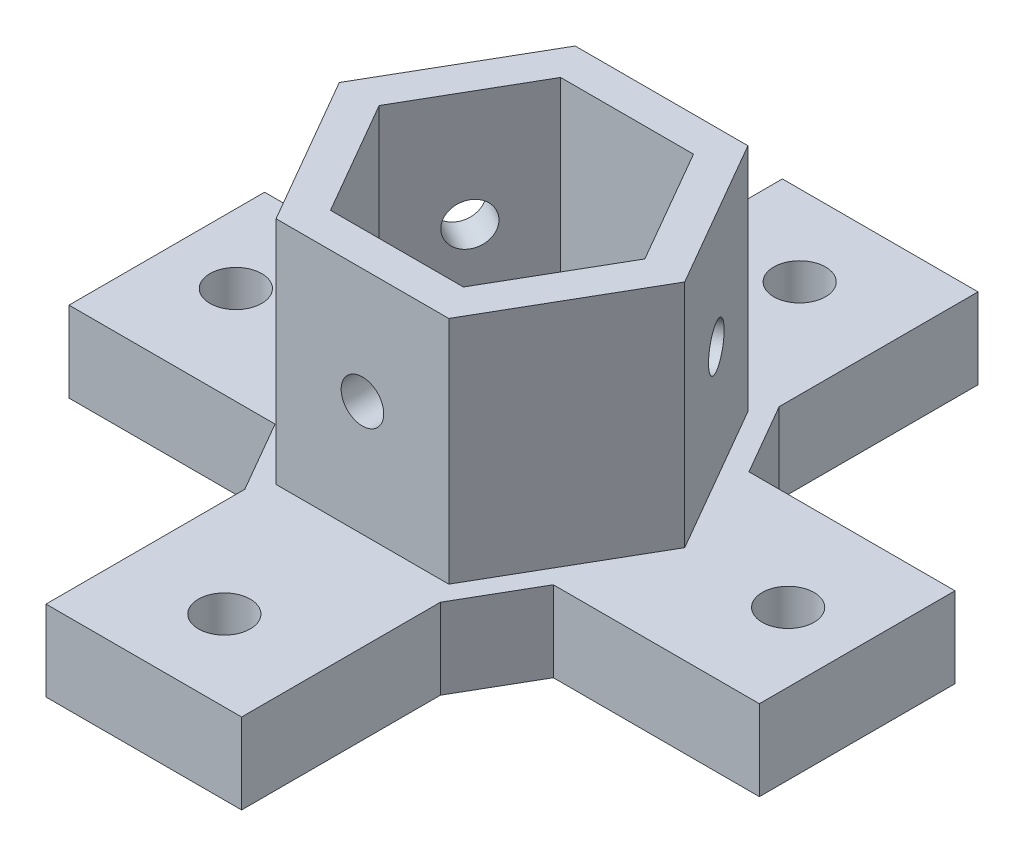
SolidWorks part; units mm, degrees
ref_plane "Front Plane" through (0, 0, 0) normal (0, 0, 1) x (1, 0, 0)
ref_plane "Top Plane" through (0, 0, 0) normal (0, 1, 0) x (1, 0, 0)
ref_plane "Right Plane" through (0, 0, 0) normal (1, 0, 0) x (0, 0, -1)
sketch "Sketch1" plane through (0, 0, 0) normal (0, 1, 0) x (1, 0, 0)
  line L0 (-8.5, 5.2678) -> (-8.5, 5.2776)
  line L1 (30, -8.5) -> (12.0208, -8.5)
  line L2 (30, -8.5) -> (30, 8.5)
  line L3 (30, 8.5) -> (12.0208, 8.5)
  line L4 (-30, -8.5) -> (-30, 8.5)
  line L5 (30, -8.5) -> (-30, 8.5) construction
  line L6 (30, 8.5) -> (-30, -8.5) construction
  line L7 (8.5, -32) -> (-8.5, -32)
  line L8 (8.5, -32) -> (8.5, -14.7224)
  line L9 (8.5, 32) -> (-8.5, 32)
  line L10 (-8.5, -32) -> (-8.5, -14.7224)
  line L11 (8.5, -32) -> (-8.5, 32) construction
  line L12 (8.5, 32) -> (-8.5, -32) construction
  line L13 (-17, 0) -> (-8.5, -14.7224)
  line L14 (-8.5, -14.7224) -> (8.5, -14.7224)
  line L15 (8.5, -14.7224) -> (17, 0)
  line L16 (17, 0) -> (8.5, 14.7224)
  line L17 (8.5, 14.7224) -> (-8.5, 14.7224)
  line L18 (-8.5, 14.7224) -> (-17, 0)
  line L19 (-11.547, 0) -> (-5.7735, -10)
  line L20 (-5.7735, -10) -> (5.7735, -10)
  line L21 (5.7735, -10) -> (11.547, 0)
  line L22 (11.547, 0) -> (5.7735, 10)
  line L23 (5.7735, 10) -> (-5.7735, 10)
  line L24 (-5.7735, 10) -> (-11.547, 0)
  line L25 (-8.5, 14.7224) -> (-8.5, 32)
  line L26 (-8.5, -5.2776) -> (-8.5, -5.2678)
  line L27 (8.5, -5.2776) -> (8.5, -5.2678)
  line L28 (8.5, 5.2678) -> (8.5, 5.2776)
  line L29 (8.5, 14.7224) -> (8.5, 32)
  line L30 (-12.0208, 8.5) -> (-30, 8.5)
  line L31 (-12.0208, -8.5) -> (-30, -8.5)
  circle A0 centre (0, 0) radius 14.7224 construction
  circle A1 centre (0, 0) radius 10 construction
  point P0 (0, 0)
  point P6 (0, 0)
  dimension "D6" = 20
  dimension "D1" = 17
  dimension "D2" = 60
  dimension "D3" = 17
  dimension "D4" = 64
  dimension "D5" = 17
extrude "Boss-Extrude1" add sketch "Sketch1" along normal blind 7
sketch "Sketch2" plane through (0, 7, 0) normal (0, 1, 0) x (1, 0, 0)
  line L1 (-15.0111, 0) -> (-7.5056, -13)
  line L2 (-7.5056, -13) -> (7.5056, -13)
  line L3 (7.5056, -13) -> (15.0111, 0)
  line L4 (15.0111, 0) -> (7.5056, 13)
  line L5 (7.5056, 13) -> (-7.5056, 13)
  line L6 (-7.5056, 13) -> (-15.0111, 0)
  line L7 (-11.547, 0) -> (-5.7735, -10)
  line L8 (-5.7735, -10) -> (5.7735, -10)
  line L9 (5.7735, -10) -> (11.547, 0)
  line L10 (11.547, 0) -> (5.7735, 10)
  line L11 (5.7735, 10) -> (-5.7735, 10)
  line L12 (-5.7735, 10) -> (-11.547, 0)
  circle A0 centre (0, 0) radius 13 construction
  circle A1 centre (0, 0) radius 10 construction
  dimension "D1" = 26
extrude "Boss-Extrude2" add sketch "Sketch2" along normal blind 20
sketch "Sketch3" plane through (0, 7, 0) normal (0, 1, 0) x (1, 0, 0)
  circle A0 centre (0, 25) radius 2.25
  dimension "D1" = 4.5
  dimension "D2" = 25
extrude "Cut-Extrude1" cut sketch "Sketch3" against normal through all
mirror "Mirror1" about plane through (0, 0, 0) normal (0, 0, 1) of "Cut-Extrude1"
sketch "Sketch4" plane through (0, 7, 0) normal (0, 1, 0) x (1, 0, 0)
  circle A0 centre (-24, 0) radius 2.25
  dimension "D1" = 4.5
  dimension "D2" = 24
extrude "Cut-Extrude2" cut sketch "Sketch4" against normal through all
mirror "Mirror2" about plane through (0, 0, 0) normal (1, 0, 0) of "Cut-Extrude2"
sketch "Sketch5" plane through (0, 0, 13) normal (0, 0, 1) x (1, 0, 0)
  line L0 (7.5056, 27) -> (-7.5056, 27) construction
  circle A0 centre (0, 17) radius 1.85
  point P2 (0, 27)
  dimension "D1" = 3.7
  dimension "D2" = 10
extrude "Cut-Extrude4" cut sketch "Sketch5" against normal up to surface (3 mm away) up to face at (0, 13.5, 10)
sketch "Sketch6" plane through (11.2583, 0, -6.5) normal (0.866, 0, -0.5) x (-0.5, 0, -0.866)
  line L0 (-7.5056, 27) -> (7.5056, 27) construction
  circle A0 centre (0, 17) radius 1.85
  point P2 (0, 27)
  dimension "D1" = 3.7
  dimension "D2" = 10
extrude "Cut-Extrude5" cut sketch "Sketch6" against normal up to surface (3 mm away) up to face at (8.6603, 13.5, -5)
sketch "Sketch7" plane through (-11.2583, 0, -6.5) normal (-0.866, 0, -0.5) x (-0.5, 0, 0.866)
  line L2 (-7.5056, 27) -> (7.5056, 27) construction
  circle A0 centre (0, 17) radius 1.85
  point P5 (0, 27)
  dimension "D1" = 3.7
  dimension "D2" = 10
extrude "Cut-Extrude6" cut sketch "Sketch7" against normal up to surface (3 mm away) up to face at (-8.6603, 13.5, -5)
equation "\"D1@Sketch4\"=\"D1@Sketch3\""
